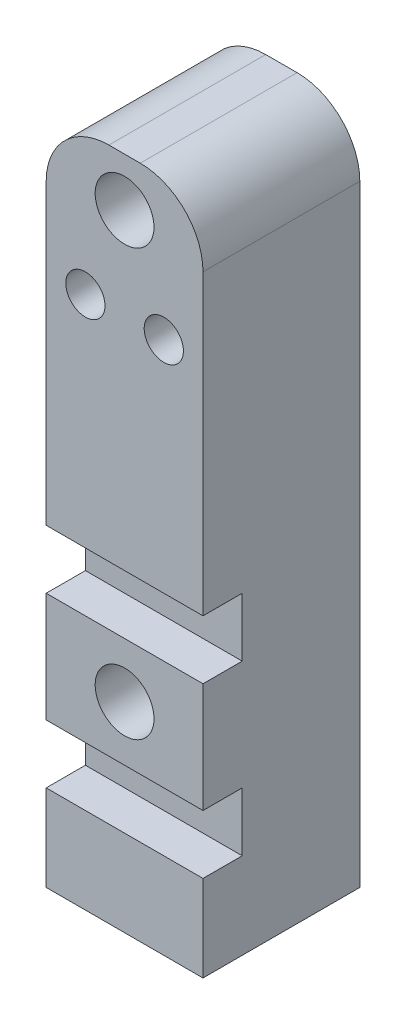
SolidWorks part; units mm, degrees
material "Plain Carbon Steel"
ref_plane "Front Plane" through (0, 0, 0) normal (0, 0, 1) x (1, 0, 0)
ref_plane "Top Plane" through (0, 0, 0) normal (0, 1, 0) x (1, 0, 0)
ref_plane "Right Plane" through (0, 0, 0) normal (1, 0, 0) x (0, 0, -1)
sketch "Sketch1" plane through (0, 0, 0) normal (1, 0, 0) x (0, 0, -1)
  line L0 (-12.7, 0) -> (12.7, 0)
  line L1 (55, 0) -> (-55, 0) construction
  line L2 (12.7, 0) -> (12.7, 109.22)
  line L3 (12.7, 109.22) -> (-12.7, 109.22)
  line L13 (0, -79.191) -> (0, 208.1505) construction
  line L14 (0, 55) -> (0, -55) construction
  line L15 (-12.7, 0) -> (-12.7, 13.97)
  line L16 (-36.2501, 32.385) -> (58.9349, 32.385) construction
  line L17 (-12.7, 41.275) -> (-6.35, 41.275)
  line L18 (-12.7, 23.495) -> (-6.35, 23.495)
  line L19 (-12.7, 50.8) -> (-6.35, 50.8)
  line L20 (-12.7, 13.97) -> (-6.35, 13.97)
  line L21 (-6.35, 50.8) -> (-6.35, 41.275)
  line L22 (-6.35, 23.495) -> (-6.35, 13.97)
  line L23 (-12.7, 50.8) -> (-12.7, 109.22)
  line L24 (-12.7, 23.495) -> (-12.7, 41.275)
  dimension "D1" = 25.4
  dimension "D2" = 32.385
  dimension "D3" = 8.89
  dimension "D4" = 9.525
  dimension "D5" = 9.525
  dimension "D6" = 6.35
  dimension "D7" = 109.22
extrude "Boss-Extrude1" add sketch "Sketch1" along normal mid plane 25.4
sketch "Sketch2" plane through (0, 0, 12.7) normal (0, 0, 1) x (1, 0, 0)
  line L0 (0, -55) -> (0, 55) construction
  line L1 (55, 0) -> (-55, 0) construction
  circle A0 centre (0, 32.385) radius 4.7625
  dimension "D1" = 9.525
  dimension "D2" = 32.385
extrude "Cut-Extrude1" cut sketch "Sketch2" against normal through all
fillet "Fillet1" radius 10.16 2 edges at (-12.7, 109.22, 0) (12.7, 109.22, 0)
sketch "Sketch3" plane through (0, 0, 12.7) normal (0, 0, 1) x (1, 0, 0)
  line L0 (0, -55) -> (0, 55) construction
  line L1 (2.54, 109.22) -> (-2.54, 109.22) construction
  line L2 (-22.0897, 86.36) -> (31.9101, 86.36) construction
  line L3 (0, 167.386) -> (0, 113.0418) construction
  line L4 (12.7, 99.06) -> (12.7, 50.8) construction
  circle A1 centre (-6.35, 86.36) radius 3.175
  circle A2 centre (6.35, 86.36) radius 3.175
  dimension "D4" = 6.35
  dimension "D5" = 6.35
  dimension "D3" = 22.86
  dimension "D6" = 6.35
extrude "Cut-Extrude2" cut sketch "Sketch3" against normal through all
sketch "Sketch4" plane through (0, 0, 0) normal (0, -1, 0) x (1, 0, 0)
  circle A0 centre (0, 0) radius 3.175
  dimension "D1" = 6.35
extrude "Cut-Extrude3" cut sketch "Sketch4" against normal blind 17.78
sketch "Sketch6" plane through (0, 0, 12.7) normal (0, 0, 1) x (1, 0, 0)
  line L0 (0, -55) -> (0, 55) construction
  line L1 (2.54, 109.22) -> (-2.54, 109.22) construction
  circle A0 centre (0, 101.346) radius 4.7625
  dimension "D2" = 9.525
  dimension "D1" = 7.874
extrude "Cut-Extrude4" cut sketch "Sketch6" against normal blind 16.51
